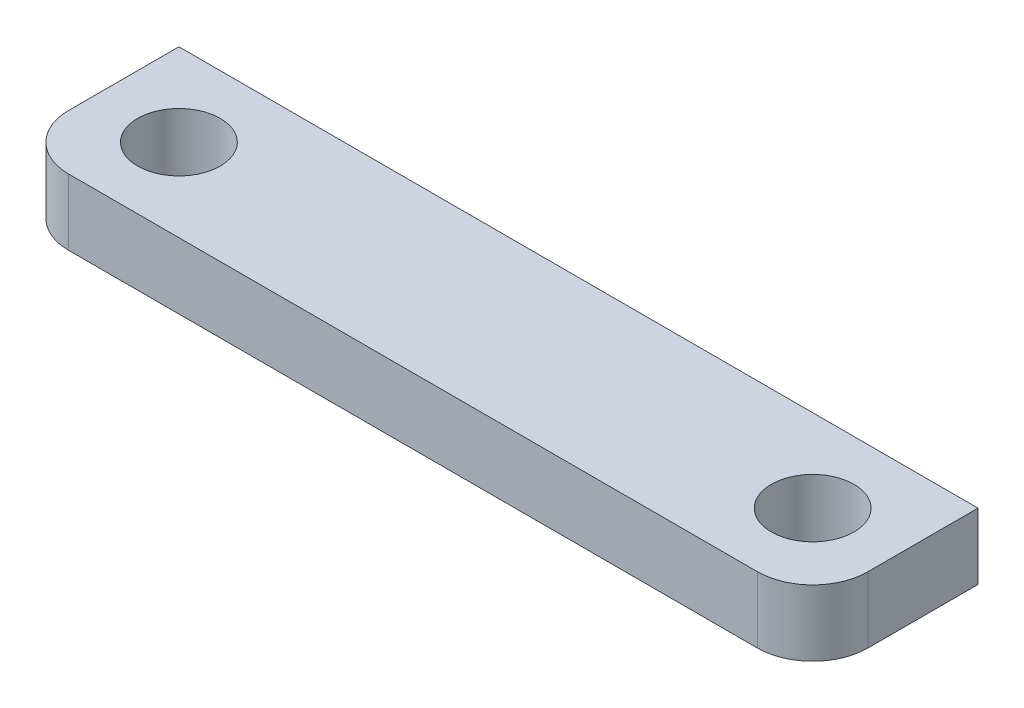
SolidWorks part; units mm, degrees
ref_plane "Front Plane" through (0, 0, 0) normal (0, 0, 1) x (1, 0, 0)
ref_plane "Top Plane" through (0, 0, 0) normal (0, 1, 0) x (1, 0, 0)
ref_plane "Right Plane" through (0, 0, 0) normal (1, 0, 0) x (0, 0, -1)
sketch "Sketch1" plane through (0, 0, 0) normal (0, 1, 0) x (1, 0, 0)
  line L0 (0, 0) -> (0, -6)
  line L1 (0, -6) -> (29, -6)
  line L2 (29, -6) -> (29, 0)
  line L3 (29, 0) -> (0, 0)
  dimension "D1" = 6
  dimension "D2" = 29
extrude "Boss-Extrude1" add sketch "Sketch1" along normal blind 2.4
sketch "Sketch2" plane through (0, 2.4, 0) normal (0, 1, 0) x (1, 0, 0)
  line L0 (0, 0) -> (0, -6) construction
  line L1 (0, -6) -> (6, -6) construction
  line L2 (0, -6) -> (29, -6) construction
  line L3 (6, -6) -> (0, 0) construction
  line L4 (29, 0) -> (29, -6) construction
  line L5 (29, 0) -> (0, 0) construction
  line L6 (29, -6) -> (23, -6) construction
  line L7 (23, -6) -> (29, 0) construction
  circle A0 centre (3, -3) radius 1.5
  circle A1 centre (26, -3) radius 1.5
  dimension "D1" = 3
extrude "Cut-Extrude1" cut sketch "Sketch2" against normal up to surface (2.4 mm away) up to face at (14.5, 0, 3)
fillet "Fillet1" radius 2 2 edges at (29, 1.2, 6) (0, 1.2, 6)
equation "\"board_length\"= 260mm"
equation "\"board_height\"= 200mm"
equation "\"board_width\"= 16.5mm"
equation "\"token_thickness\"= 7mm"
equation "\"token_diameter\"= 32mm"
equation "\"board_side_lower_height\"= 55mm"
equation "\"board_side_height\"= 156.5mm"
equation "\"board_side_length\"= 100mm"
equation "\"board_slot_width\"= \"board_length\" / 7"
equation "\"token_ridge\"= ( \"token_thickness\" - 4mm ) / 2"
equation "\"token_ridge_width\"= 1.5mm"
equation "\"25T_outer_diameter\"= 20mm"
equation "\"25T_inner_diameter\"= 9mm"
equation "\"2T_screw_distance\"= 14mm"
equation "\"2T_outer_thickness\"= 2mm"
equation "\"2T_inner_thickness\"= 4.5mm"
equation "\"MG996R_outer_length\"= 54mm"
equation "\"MG996R_inner_length\"= 40mm"
equation "\"MG996R_width\"= 20mm"
equation "\"MG996R_height\"= 26.6mm"
equation "\"MG996R_full_height\"= 45.7mm"
equation "\"MG996R_full_width\"= 55.5mm"
equation "\"MG996R_screw_distance\"= 10mm"
equation "\"magnet_diameter\"= 10mm"
equation "\"magnet_thickness\"= 2mm"
equation "\"dispenser_barrel_margin\"= 2.5mm"
equation "\"dispenser_wheel_width\"= \"token_thickness\" + 5mm"
equation "\"dispenser_cover_margin\"= 3.0mm"
equation "\"dispenser_cover_thickness\"= 5.0mm"
equation "\"MG996R_major_axis_distance\"= 34.3mm"
equation "\"MG996R_major_screw_distance\"= 48.6mm"
equation "\"MG996R_minor_screw_distance\"= 9.9mm"
equation "\"MG996R_mid_height\"= 37.5mm"
equation "\"dispenser_slope\"= 30deg"
equation "\"dispenser_cover_length\"= 16mm"
equation "\"dispenser_carrier_width\"= 3.5mm"
equation "\"dispenser_carrier_height\"= 50mm"
equation "\"carrier_width\"= \"shaft_diameter\" * 2"
equation "\"shaft_diameter\"= 8mm"
equation "\"carrier_thickness\"=16mm"
equation "\"GT2_width\"= 7mm"
equation "\"GT2_outer_diameter\"= 18mm"
equation "\"GT2_inner_diameter\"= 12mm"
equation "\"GT2_pitch_diameter\"= 2mm"
equation "\"GT2_tooth_height\"= 1.6mm"
equation "\"GT2_upper_length\"= 0.6mm"
equation "\"belt_holder_width\"= \"GT2_width\" + 2 * 6mm"
equation "\"carrier_screw_distance\"= \"dispenser_cover_thickness\" + 3 * 6mm"
equation "\"magnetometer_offset\"= 6mm"
equation "\"magnetometer_width\"= 15mm"
equation "\"magnetometer_length\"= 19mm"
equation "\"magnetometer_thickness\" = 2.5mm"
equation "\"timing_belt_gap\"= 2.5mm"
equation "\"carrier_height_top\"= 6mm + \"carrier_thickness\" + 0.5mm"
equation "\"carrier_height_bot\"= 6mm + \"carrier_thickness\" + \"GT2_inner_diameter\" + 1.0mm + \"timing_belt_gap\""
equation "\"D5@Sketch3\"=\"magnetometer_thickness\""
equation "\"D1@Sketch1\"=(\"GT2_width\"-\"GT2_width\"+2*6mm)/2"
equation "\"D2@Sketch1\"=\"carrier_screw_distance\"+6mm"
